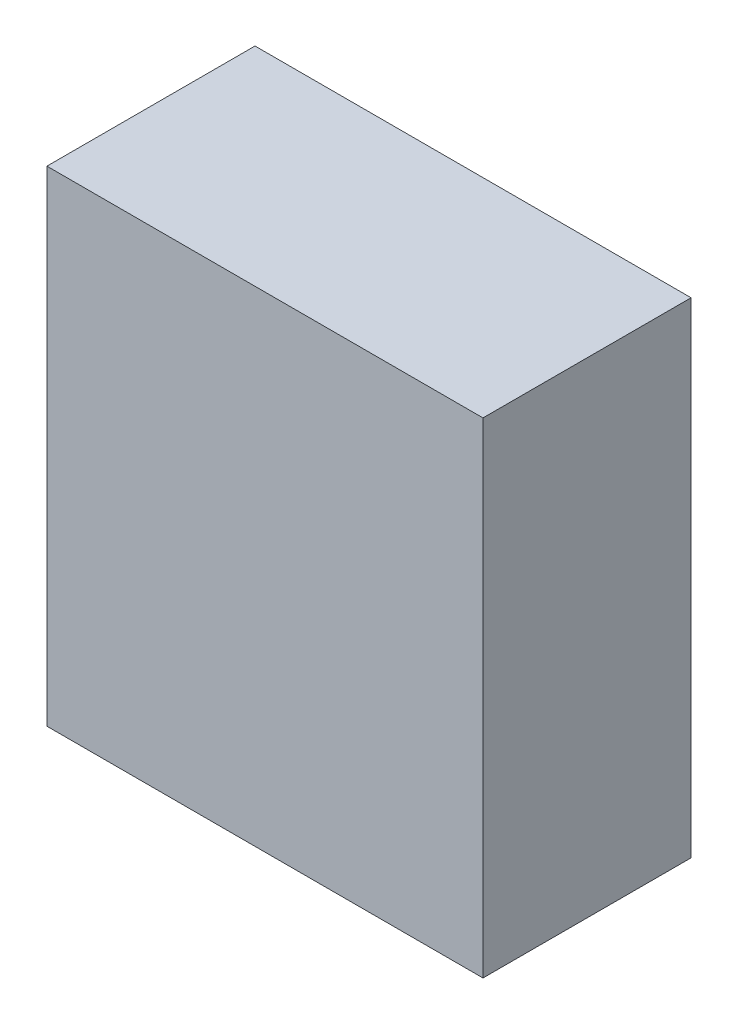
SolidWorks part; units mm, degrees
ref_plane "Front Plane" through (0, 0, 0) normal (0, 0, 1) x (1, 0, 0)
ref_plane "Top Plane" through (0, 0, 0) normal (0, 1, 0) x (1, 0, 0)
ref_plane "Right Plane" through (0, 0, 0) normal (1, 0, 0) x (0, 0, -1)
sketch "Sketch1" plane through (0, 0, 0) normal (0, 0, 1) x (1, 0, 0)
  line L1 (-64.2938, -72.2313) -> (64.2937, -72.2313)
  line L2 (-64.2938, -72.2313) -> (-64.2938, 72.2313)
  line L3 (-64.2938, 72.2313) -> (64.2937, 72.2313)
  line L4 (64.2937, -72.2313) -> (64.2937, 72.2313)
  line L5 (-64.2938, -72.2313) -> (64.2937, 72.2313) construction
  line L6 (-64.2938, 72.2313) -> (64.2937, -72.2313) construction
  point P0 (0, 0)
  dimension "D1" = 128.5875
  dimension "D2" = 144.4625
extrude "Boss-Extrude1" add sketch "Sketch1" against normal blind 61.0718 contours L3 L4 L1 L2
shell "Shell1" thickness 6.35
